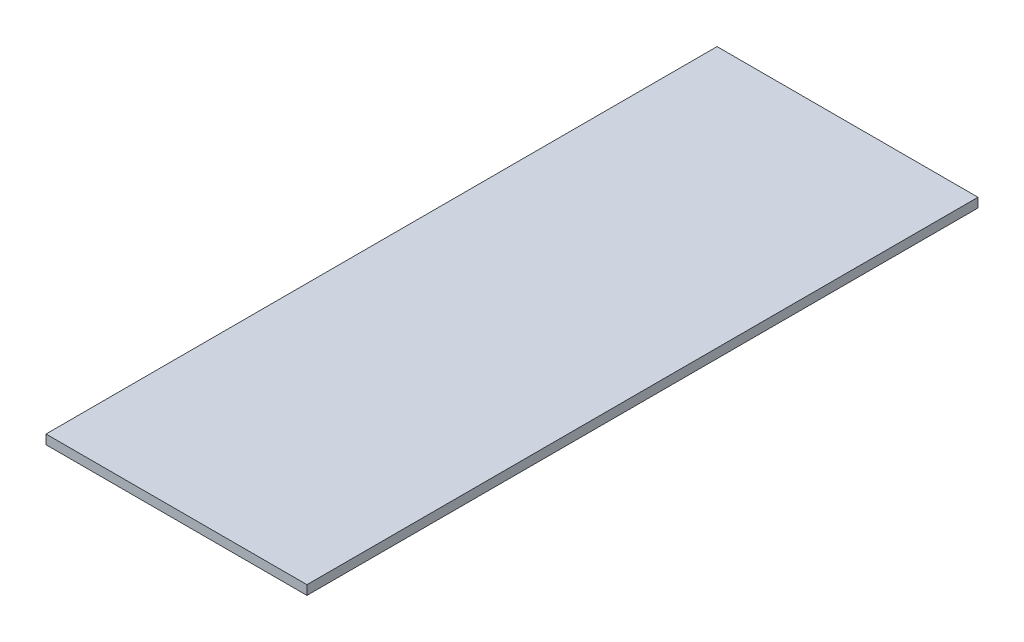
SolidWorks part; units mm, degrees
ref_plane "Front Plane" through (0, 0, 0) normal (0, 0, 1) x (1, 0, 0)
ref_plane "Top Plane" through (0, 0, 0) normal (0, 1, 0) x (1, 0, 0)
ref_plane "Right Plane" through (0, 0, 0) normal (1, 0, 0) x (0, 0, -1)
sketch "Sketch1" plane through (0, 0, 0) normal (0, 1, 0) x (1, 0, 0)
  line L1 (-36.9372, 30.1056) -> (51.9628, 30.1056)
  line L2 (-36.9372, 30.1056) -> (-36.9372, -198.4944)
  line L3 (-36.9372, -198.4944) -> (51.9628, -198.4944)
  line L4 (51.9628, 30.1056) -> (51.9628, -198.4944)
  dimension "D1" = 88.9
  dimension "D2" = 228.6
extrude "Boss-Extrude1" add sketch "Sketch1" along normal blind 3.175
